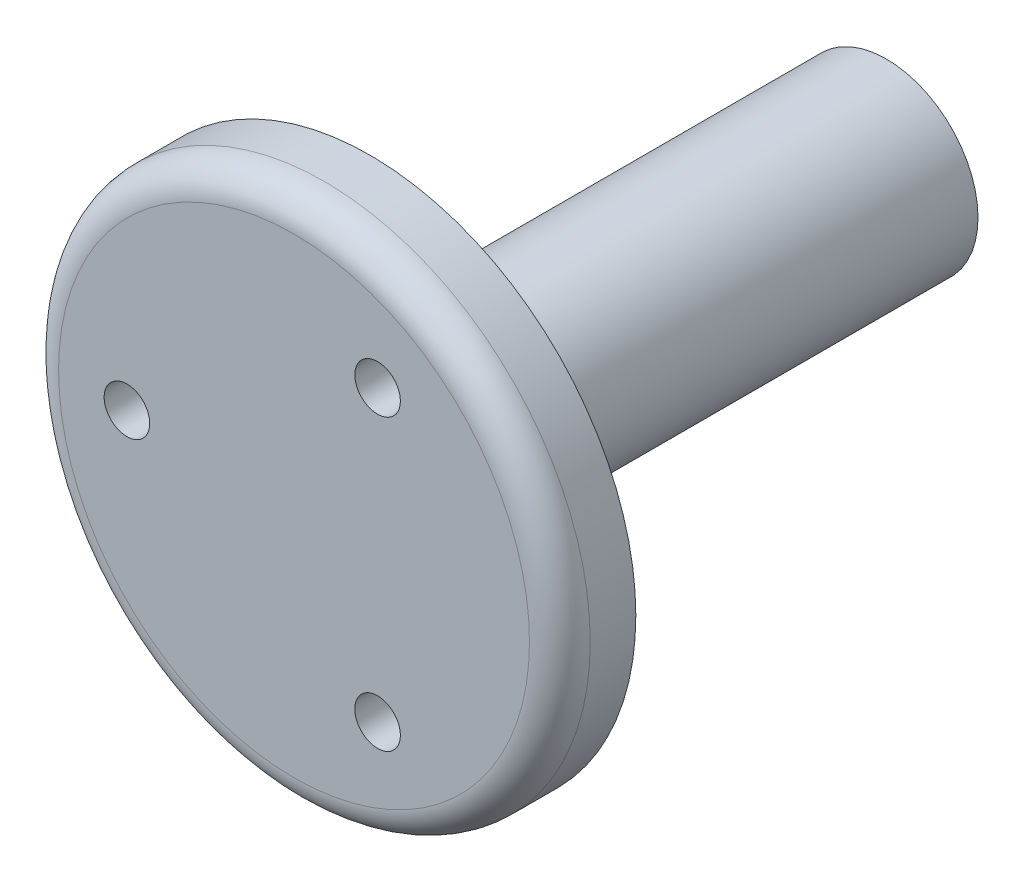
SolidWorks part; units mm, degrees
material "Plastique personnalisé"
ref_plane "Plan de face" through (0, 0, 0) normal (0, 0, 1) x (1, 0, 0)
ref_plane "Plan de dessus" through (0, 0, 0) normal (0, 1, 0) x (1, 0, 0)
ref_plane "Plan de droite" through (0, 0, 0) normal (1, 0, 0) x (0, 0, -1)
sketch "Esquisse1" plane through (0, 0, 0) normal (0, 0, 1) x (1, 0, 0)
  circle A0 centre (0, 0) radius 6.025
  dimension "D1" = 12.05
extrude "Boss.-Extru.1" add sketch "Esquisse1" along normal blind 34
sketch "Esquisse2" plane through (0, 0, 34) normal (0, 0, 1) x (1, 0, 0)
  circle A0 centre (0, 0.0468) radius 17.5
  dimension "D1" = 35
extrude "Boss.-Extru.2" add sketch "Esquisse2" along normal blind 5
sketch "Esquisse4" plane through (0, 0, 39) normal (0, 0, 1) x (1, 0, 0)
  line L0 (0, 0) -> (-11, 0) construction
  circle A0 centre (-11, 0) radius 1.5
  circle A1 centre (5.5, 9.5263) radius 1.5
  circle A2 centre (5.5, -9.5263) radius 1.5
  point P11 (0, 0)
  dimension "D2" = 3
  dimension "D1" = 11
extrude "Enlèv. mat.-Extru.1" cut sketch "Esquisse4" against normal blind 10
fillet "Congé1" radius 2 1 edges at (17.5, 0.0468, 39)
sketch "Esquisse5" plane through (0, 0, 0) normal (0, 0, -1) x (-1, 0, 0)
  line L0 (0, 2.98) -> (0, -2.56) construction
  line L1 (0, -2.56) -> (-1.5254, -2.56) construction
  line L2 (0, -2.56) -> (1.5254, -2.56) construction
  line L3 (1.5254, -2.56) -> (-1.5254, -2.56)
  arc A1 (1.5254, -2.56) -> (-1.5254, -2.56) centre (0, -0.0009) ccw
  dimension "D1" = 5.54
extrude "Enlèv. mat.-Extru.2" cut sketch "Esquisse5" against normal blind 15
sketch "Esquisse6" plane through (0, 0, 0) normal (0, 1, 0) x (1, 0, 0)
  line L0 (0, 0) -> (0, -3) construction
  circle A0 centre (0, -3) radius 1.5
  dimension "D1" = 3
extrude "Enlèv. mat.-Extru.3" cut sketch "Esquisse6" against normal blind 7
